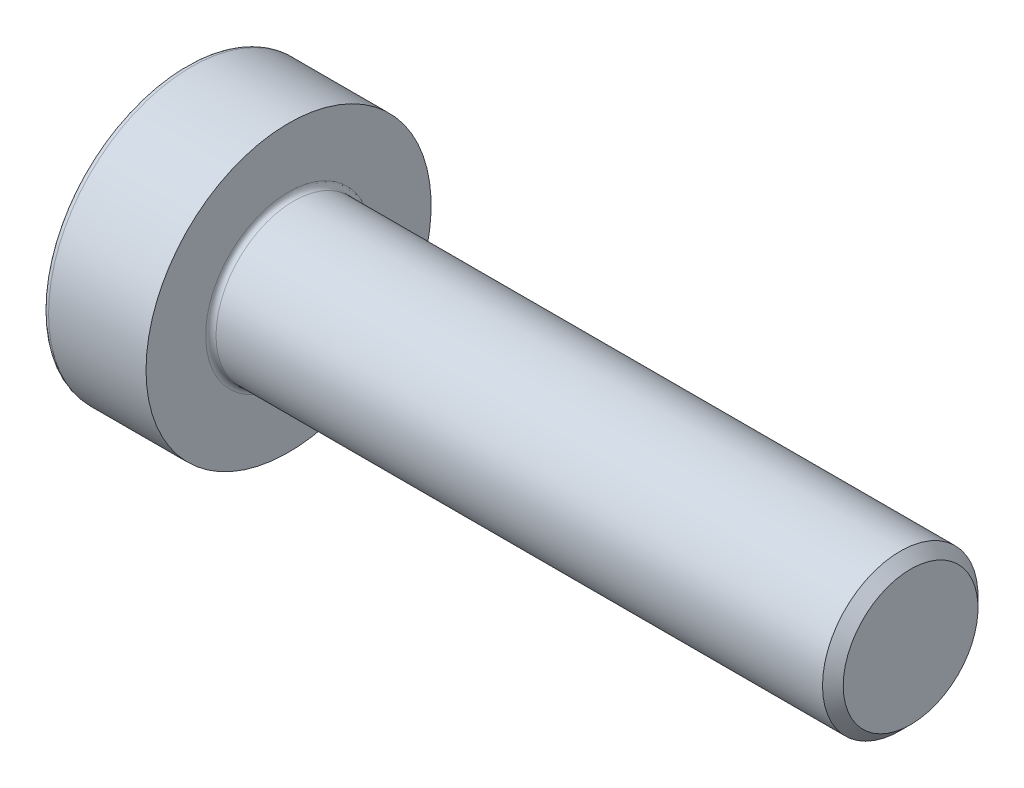
SolidWorks part; units mm, degrees
material "AISI Тип A2 Инструментальная сталь"
ref_plane "Front Plane" through (0, 0, 0) normal (0, 0, 1) x (1, 0, 0)
ref_plane "Top Plane" through (0, 0, 0) normal (0, 1, 0) x (1, 0, 0)
ref_plane "Right Plane" through (0, 0, 0) normal (1, 0, 0) x (0, 0, -1)
sketch "Sketch1" plane through (0, 0, 0) normal (0, 0, 1) x (1, 0, 0)
  line L0 (0, 0) -> (0, 2.75)
  line L1 (0, 2.75) -> (2, 2.75)
  line L2 (2, 2.75) -> (2, 0)
  line L3 (0, 0) -> (4.2799, 0) construction
  line L4 (2, 0) -> (14, 0)
  line L5 (14, 0) -> (14, 1.5)
  line L6 (14, 1.5) -> (2, 1.5)
  dimension "D1" = 12
  dimension "D2" = 2
  dimension "D3" = 2.75
  dimension "D4" = 1.5
revolve "Revolve1" add sketch "Sketch1" angle 360 about L3
fillet "Fillet1" radius 0.1 1 edges at (2, 0, 1.5)
fillet "Fillet2" radius 0.12 1 edges at (0, 0, 2.75)
chamfer "Chamfer1" distance 0.2 angle 45 1 edges at (14, 0, 1.5)
sketch "Sketch2" plane through (0, 0, 0) normal (-1, 0, 0) x (0, 0, 1)
  line L1 (0, 1.4434) -> (-1.25, 0.7217)
  line L2 (-1.25, 0.7217) -> (-1.25, -0.7217)
  line L3 (-1.25, -0.7217) -> (0, -1.4434)
  line L4 (0, -1.4434) -> (1.25, -0.7217)
  line L5 (1.25, -0.7217) -> (1.25, 0.7217)
  line L6 (1.25, 0.7217) -> (0, 1.4434)
  circle A0 centre (0, 0) radius 1.25 construction
extrude "Extrude1" cut sketch "Sketch2" against normal blind 1
